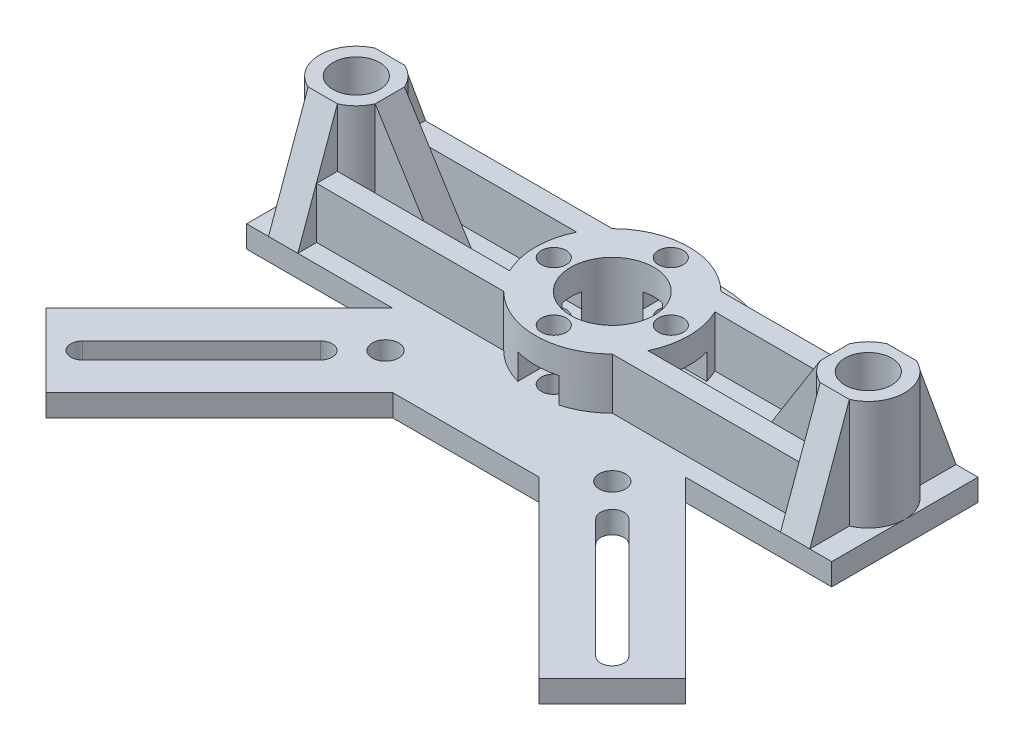
SolidWorks part; units mm, degrees
ref_plane "前视基准面" through (0, 0, 0) normal (0, 0, 1) x (1, 0, 0)
ref_plane "上视基准面" through (0, 0, 0) normal (0, 1, 0) x (1, 0, 0)
ref_plane "右视基准面" through (0, 0, 0) normal (1, 0, 0) x (0, 0, -1)
sketch "草图1" plane through (0, 0, 0) normal (0, 1, 0) x (1, 0, 0)
  line L0 (-35.0818, -10) -> (-40, -10)
  line L1 (-40, -10) -> (-40, 10)
  line L2 (-40, 10) -> (-11.1803, 10)
  line L3 (-10, -20) -> (10, -20)
  line L4 (40, 10) -> (40, -10)
  line L5 (40, -10) -> (20, -10)
  line L6 (-20, -10) -> (-43.7132, -33.7132)
  line L7 (-10, -20) -> (-33.7132, -43.7132)
  line L8 (10, -20) -> (33.8446, -43.8446)
  line L9 (20, -10) -> (43.8446, -33.8446)
  line L10 (-43.7132, -33.7132) -> (-33.7132, -43.7132)
  line L11 (33.8446, -43.8446) -> (43.8446, -33.8446)
  line L12 (-19.9497, -19.9497) -> (-36.2132, -36.2132) construction
  line L13 (-18.8184, -21.0811) -> (-35.0818, -37.3446)
  line L14 (-21.0811, -18.8184) -> (-37.3446, -35.0818)
  line L15 (19.9497, -19.9497) -> (36.2132, -36.2132) construction
  line L16 (21.0811, -18.8184) -> (37.3446, -35.0818)
  line L17 (18.8184, -21.0811) -> (35.0818, -37.3446)
  line L18 (11.1803, 10) -> (40, 10)
  line L19 (-35.0818, -10) -> (-20, -10)
  circle A0 centre (35, 0) radius 3.2
  circle A2 centre (-15.5, -15.5) radius 1.8
  circle A3 centre (15.5, -15.5) radius 1.8
  circle A4 centre (-35, 0) radius 3.2
  arc A6 (-18.8184, -21.0811) -> (-21.0811, -18.8184) centre (-19.9497, -19.9497) ccw
  arc A7 (-37.3446, -35.0818) -> (-35.0818, -37.3446) centre (-36.2132, -36.2132) ccw
  circle A8 centre (0, 0) radius 5.7
  circle A9 centre (-8, 0) radius 1.7
  circle A10 centre (0, 8) radius 1.7
  circle A11 centre (8, 0) radius 1.7
  circle A12 centre (0, -8) radius 1.7
  arc A13 (21.0811, -18.8184) -> (18.8184, -21.0811) centre (19.9497, -19.9497) ccw
  arc A14 (35.0818, -37.3446) -> (37.3446, -35.0818) centre (36.2132, -36.2132) ccw
  arc A17 (11.1803, 10) -> (-11.1803, 10) centre (0, 0) ccw
  point P34 (-33.1606, -34.0237)
  point P38 (-28.0815, -28.0815)
  point P43 (28.0815, -28.0815)
extrude "凸台-拉伸1" add sketch "草图1" along normal blind 3
sketch "草图2" plane through (0, 3, 0) normal (0, 1, 0) x (1, 0, 0)
  circle A0 centre (0, 0) radius 10.5
extrude "凸台-拉伸2" add sketch "草图2" along normal blind 7
sketch "草图4" plane through (0, 3, 0) normal (0, -1, 0) x (1, 0, 0)
  circle A1 centre (0, -8) radius 1.7
  circle A2 centre (-8, 0) radius 1.7
  circle A3 centre (8, 0) radius 1.7
  circle A4 centre (0, 8) radius 1.7
extrude "切除-拉伸1" cut sketch "草图4" against normal blind 7
sketch "草图5" plane through (0, 3, 0) normal (0, 1, 0) x (1, 0, 0)
  line L1 (-4.7668, 0) -> (-6.3834, 2.8)
  line L2 (-6.3834, 2.8) -> (-11.2332, 2.8)
  line L5 (-11.2332, -2.8) -> (-6.3834, -2.8)
  line L6 (-6.3834, -2.8) -> (-4.7668, 0)
  line L7 (4.7668, 0) -> (6.3834, -2.8)
  line L8 (6.3834, -2.8) -> (11.2332, -2.8)
  line L11 (11.2332, 2.8) -> (6.3834, 2.8)
  line L12 (6.3834, 2.8) -> (4.7668, 0)
  line L14 (-2.8, 11.2332) -> (-2.8, 6.3834)
  line L15 (-2.8, 6.3834) -> (0, 4.7668)
  line L16 (0, 4.7668) -> (2.8, 6.3834)
  line L17 (2.8, 6.3834) -> (2.8, 11.2332)
  line L19 (0, -4.7668) -> (-2.8, -6.3834)
  line L20 (-2.8, -6.3834) -> (-2.8, -11.2332)
  line L23 (2.8, -11.2332) -> (2.8, -6.3834)
  line L24 (2.8, -6.3834) -> (0, -4.7668)
  line L25 (-11.2332, 2.8) -> (-11.2332, -2.8)
  line L29 (-2.8, 11.2332) -> (2.8, 11.2332)
  line L32 (11.2332, 2.8) -> (11.2332, -2.8)
  line L35 (-2.8, -11.2332) -> (2.8, -11.2332)
  line L39 (-1.4, -10.4249) -> (0, -11.2332) [skipped]
  line L40 (1.4, -10.4249) -> (2.8, -9.6166) [skipped]
  line L41 (9.6166, -2.8) -> (10.4249, -1.4) [skipped]
  line L42 (11.2332, 0) -> (10.4249, 1.4) [skipped]
  line L43 (1.4, 10.4249) -> (0, 11.2332) [skipped]
  line L44 (0, 11.2332) -> (-1.4, 10.4249) [skipped]
  line L45 (-10.4249, -1.4) -> (-9.6166, -2.8) [skipped]
  line L46 (-9.6166, 2.8) -> (-10.4249, 1.4) [skipped]
extrude "切除-拉伸2" cut sketch "草图5" along normal blind 3.5
sketch "草图6" plane through (0, 3, 0) normal (0, -1, 0) x (1, 0, 0)
  circle A0 centre (0, 0) radius 5.7
extrude "切除-拉伸3" cut sketch "草图6" against normal blind 20
sketch "草图7" plane through (0, 3, 0) normal (0, 1, 0) x (1, 0, 0)
  circle A0 centre (-35, 0) radius 3.2
  circle A1 centre (-35, 0) radius 5
  circle A2 centre (35, 0) radius 3.2
  circle A3 centre (35, 0) radius 5
extrude "凸台-拉伸3" add sketch "草图7" along normal blind 15
sketch "草图8" plane through (0, 3, 0) normal (0, 1, 0) x (1, 0, 0)
  line L0 (-11.1803, 10) -> (-40, 10) construction
  line L1 (-31, -2) -> (-21, -2)
  line L2 (-31, -2) -> (-31, 2)
  line L3 (-31, 2) -> (-21, 2)
  line L4 (-21, -2) -> (-21, 2)
  line L5 (-33, 4) -> (-37, 4)
  line L6 (-33, 4) -> (-33, 10)
  line L7 (-33, 10) -> (-37, 10)
  line L8 (-37, 4) -> (-37, 10)
  line L9 (-40, -10) -> (-20, -10) construction
  line L10 (-37, -4) -> (-33, -4)
  line L11 (-37, -4) -> (-37, -10)
  line L12 (-37, -10) -> (-33, -10)
  line L13 (-33, -4) -> (-33, -10)
  line L14 (40, 10) -> (11.1803, 10) construction
  line L15 (31, 2) -> (21, 2)
  line L16 (31, 2) -> (31, -2)
  line L17 (31, -2) -> (21, -2)
  line L18 (21, 2) -> (21, -2)
  line L19 (33, 4) -> (37, 4)
  line L20 (33, 4) -> (33, 10)
  line L21 (33, 10) -> (37, 10)
  line L22 (37, 4) -> (37, 10)
  line L23 (20, -10) -> (40, -10) construction
  line L24 (33, -4) -> (37, -4)
  line L25 (33, -4) -> (33, -10)
  line L26 (33, -10) -> (37, -10)
  line L27 (37, -4) -> (37, -10)
extrude "凸台-拉伸4" add sketch "草图8" along normal blind 15
sketch "草图9" plane through (0, 0, 2) normal (0, 0, 1) x (1, 0, 0)
  line L0 (-30.4174, 18) -> (-21, 3)
  line L1 (-30.4174, 18) -> (-21, 18)
  line L2 (-30.4174, 18) -> (-21, 18) construction
  line L3 (-21, 18) -> (-21, 3)
  line L4 (21, 3) -> (30.4174, 18)
  line L5 (30.4174, 18) -> (21, 18)
  line L6 (21, 18) -> (21, 3)
extrude "切除-拉伸4" cut sketch "草图9" against normal blind 15
sketch "草图10" plane through (33, 0, 0) normal (-1, 0, 0) x (0, 0, 1)
  line L0 (-4.5826, 18) -> (-10, 3)
  line L1 (-10, 18) -> (-10, 3) construction
  line L2 (-10, 3) -> (-10, 18)
  line L3 (-10, 18) -> (-4.5826, 18) construction
  line L4 (-10, 18) -> (-4.5826, 18)
  line L5 (4.5826, 18) -> (10, 18)
  line L6 (10, 18) -> (10, 3)
  line L7 (4.5826, 3) -> (10, 3) construction
  line L8 (10, 18) -> (10, 3) construction
  line L9 (10, 3) -> (4.5826, 18)
extrude "切除-拉伸5" cut sketch "草图10" against normal blind 15
sketch "草图11" plane through (-33, 0, 0) normal (1, 0, 0) x (0, 0, -1)
  line L0 (-4.5826, 18) -> (-10, 3)
  line L1 (-10, 3) -> (-10, 18)
  line L2 (-10, 18) -> (-4.5826, 18)
  line L3 (4.5826, 18) -> (10, 3)
  line L4 (10, 3) -> (10, 18)
  line L5 (10, 18) -> (4.5826, 18)
extrude "切除-拉伸6" cut sketch "草图11" against normal blind 15
sketch "草图12" plane through (0, 3, 0) normal (0, 1, 0) x (1, 0, 0)
  line L1 (-33, -4.5826) -> (-7.4246, -4.5826)
  line L2 (-33, -4.5826) -> (-33, -7.4246)
  line L3 (-33, -7.4246) -> (-7.4246, -7.4246)
  line L4 (-7.4246, -4.5826) -> (-7.4246, -7.4246)
  line L5 (-33, 4.5826) -> (-7.4246, 4.5826)
  line L6 (-33, 4.5826) -> (-33, 7.4246)
  line L7 (-33, 7.4246) -> (-7.4246, 7.4246)
  line L8 (-7.4246, 4.5826) -> (-7.4246, 7.4246)
  line L9 (33, 4.5826) -> (7.4246, 4.5826)
  line L10 (33, 4.5826) -> (33, 7.4246)
  line L11 (33, 7.4246) -> (7.4246, 7.4246)
  line L12 (7.4246, 4.5826) -> (7.4246, 7.4246)
  line L13 (33, -4.5826) -> (7.4246, -4.5826)
  line L14 (33, -4.5826) -> (33, -7.4246)
  line L15 (33, -7.4246) -> (7.4246, -7.4246)
  line L16 (7.4246, -4.5826) -> (7.4246, -7.4246)
  arc A0 (-10.1198, -2.8) -> (-2.8, -10.1198) centre (0, 0) ccw construction
  arc A1 (-2.8, 10.1198) -> (-10.1198, 2.8) centre (0, 0) ccw construction
  arc A2 (10.1198, 2.8) -> (2.8, 10.1198) centre (0, 0) ccw construction
  arc A3 (2.8, -10.1198) -> (10.1198, -2.8) centre (0, 0) ccw construction
extrude "凸台-拉伸5" add sketch "草图12" along normal blind 7
